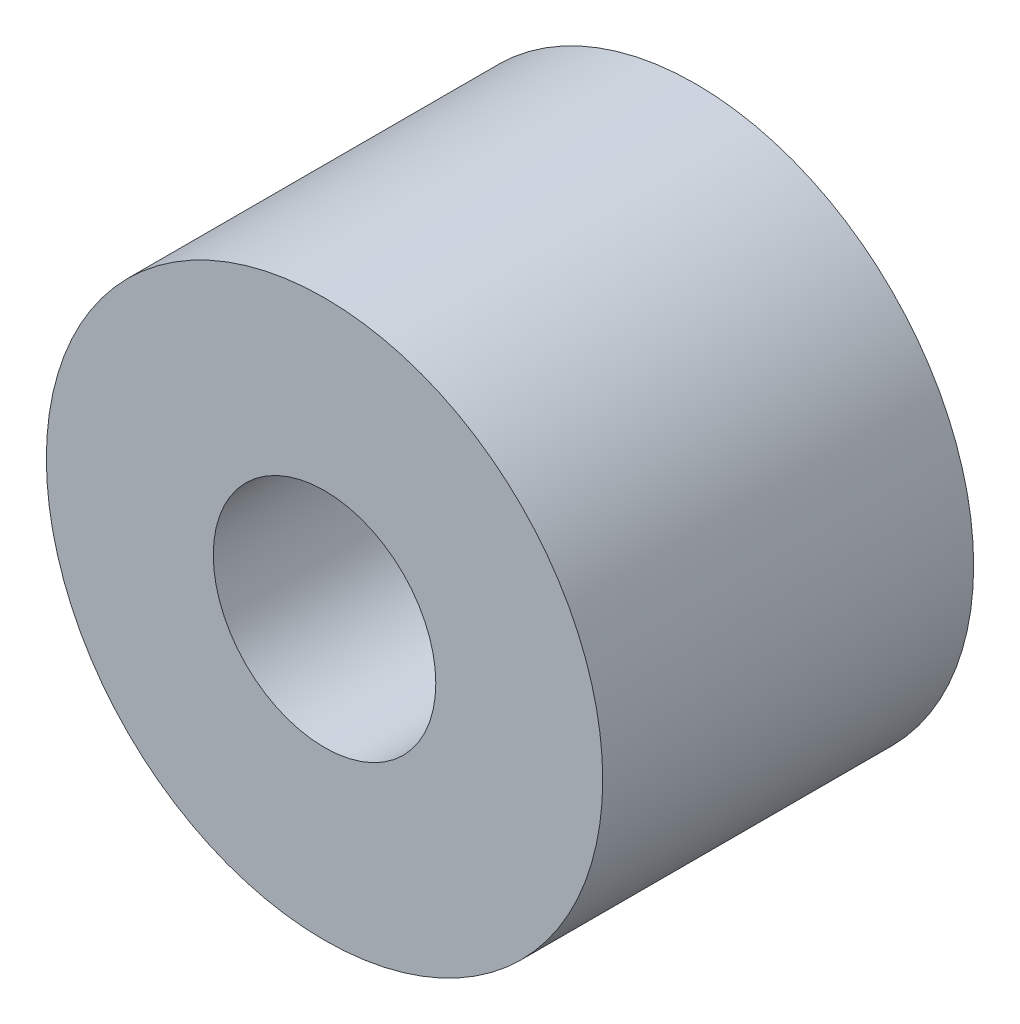
SolidWorks part; units mm, degrees
ref_plane "Piano frontale" through (0, 0, 0) normal (0, 0, 1) x (1, 0, 0)
ref_plane "Piano superiore" through (0, 0, 0) normal (0, 1, 0) x (1, 0, 0)
ref_plane "Piano destro" through (0, 0, 0) normal (1, 0, 0) x (0, 0, -1)
sketch "Schizzo1" plane through (0, 0, 0) normal (0, 0, 1) x (1, 0, 0)
  circle A0 centre (0, 0) radius 22.5
  circle A1 centre (0, 0) radius 9
  dimension "D1" = 45
  dimension "D2" = 18
extrude "Estrusione-Estrusione1" add sketch "Schizzo1" along normal blind 30
sketch "Schizzo3" plane through (0, 0, 0) normal (0, 1, 0) x (1, 0, 0)
  line L0 (9, 0) -> (-9, 0) construction
  circle A0 centre (0, -10) radius 3
  dimension "D1" = 6
  dimension "D2" = 10
extrude "Estrusione-Estrusione2" add sketch "Schizzo3" against normal blind 25 contours A0
sketch "Schizzo4" plane through (0, 0, 30) normal (0, 0, 1) x (1, 0, 0)
  circle A0 centre (0, 0) radius 9
extrude "Taglio-Estrusione1" cut sketch "Schizzo4" against normal blind 40
